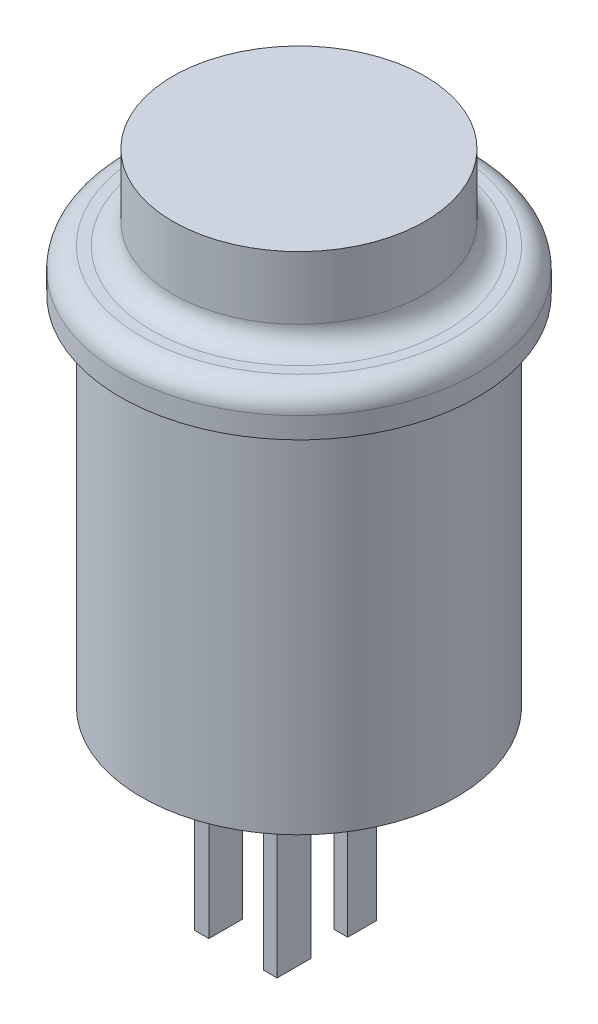
SolidWorks part; units mm, degrees
ref_plane "Ön Düzlem" through (0, 0, 0) normal (0, 0, 1) x (1, 0, 0)
ref_plane "Üst Düzlem" through (0, 0, 0) normal (0, 1, 0) x (1, 0, 0)
ref_plane "Sağ Düzlem" through (0, 0, 0) normal (1, 0, 0) x (0, 0, -1)
sketch "Çizim1" plane through (0, 0, 0) normal (0, 1, 0) x (1, 0, 0)
  circle A0 centre (0, 0) radius 6
  dimension "D1" = 12
extrude "Yükseklik-Ekstrüzyon1" add sketch "Çizim1" along normal blind 4
sketch "Çizim2" plane through (0, 0, 0) normal (0, -1, 0) x (1, 0, 0)
  circle A0 centre (0, 0) radius 8.5
  point P0 (0, 0)
extrude "Yükseklik-Ekstrüzyon2" add sketch "Çizim2" along normal blind 2
fillet "Radyus1" radius 1 2 edges at (0, 0, -6) (0, 0, -8.5)
sketch "Çizim3" plane through (0, -2, 0) normal (0, -1, 0) x (1, 0, 0)
  circle A0 centre (0, 0) radius 7.5
extrude "Yükseklik-Ekstrüzyon3" add sketch "Çizim3" along normal blind 17
sketch "Çizim4" plane through (0, -19, 0) normal (0, -1, 0) x (1, 0, 0)
  line L1 (3.0316, 4.73) -> (3.6891, 4.73)
  line L2 (3.0316, 4.73) -> (3.0316, 3.1229)
  line L3 (3.0316, 3.1229) -> (3.6891, 3.1229)
  line L4 (3.6891, 4.73) -> (3.6891, 3.1229)
  line L5 (-0.2557, 4.73) -> (0.4383, 4.73)
  line L6 (-0.2557, 4.73) -> (-0.2557, 3.1229)
  line L7 (-0.2557, 3.1229) -> (0.4383, 3.1229)
  line L8 (0.4383, 4.73) -> (0.4383, 3.1229)
  line L9 (3.0316, 1.3697) -> (3.6891, 1.3697)
  line L10 (3.0316, 1.3697) -> (3.0316, 0)
  line L11 (3.0316, 0) -> (3.6891, 0)
  line L12 (3.6891, 1.3697) -> (3.6891, 0)
  line L13 (-0.2557, 1.3697) -> (0.4383, 1.3697)
  line L14 (-0.2557, 1.3697) -> (-0.2557, 0)
  line L15 (-0.2557, 0) -> (0.4383, 0)
  line L16 (0.4383, 1.3697) -> (0.4383, 0)
extrude "Yükseklik-Ekstrüzyon4" add sketch "Çizim4" along normal blind 7
